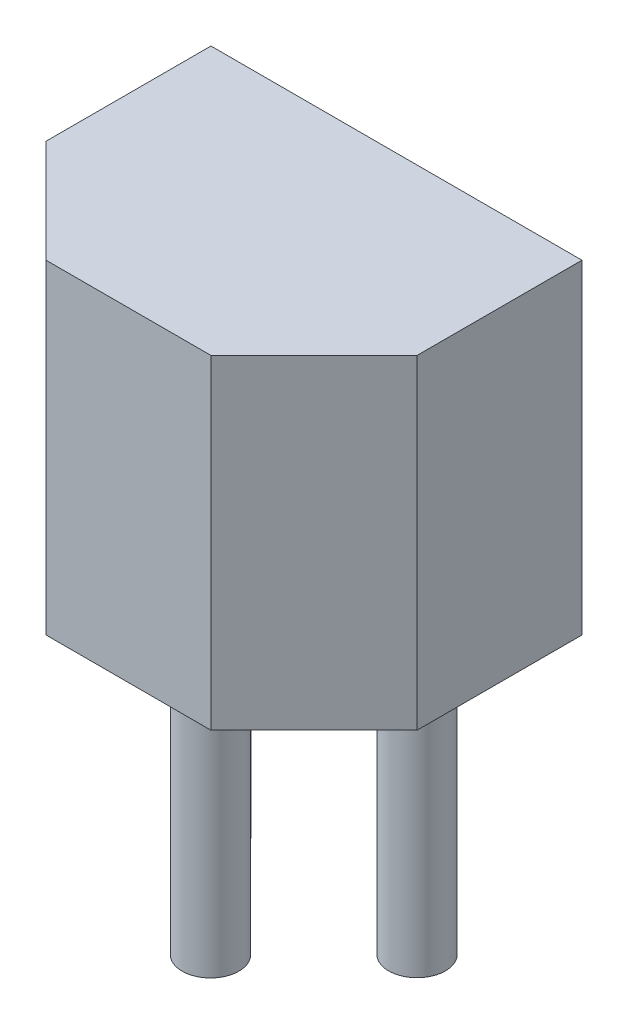
SolidWorks part; units mm, degrees
ref_plane "Front Plane" through (0, 0, 0) normal (0, 0, 1) x (1, 0, 0)
ref_plane "Top Plane" through (0, 0, 0) normal (0, 1, 0) x (1, 0, 0)
ref_plane "Right Plane" through (0, 0, 0) normal (1, 0, 0) x (0, 0, -1)
sketch "Sketch1" plane through (0, 0, 0) normal (0, 1, 0) x (1, 0, 0)
  line L0 (-1.016, -1.016) -> (0.254, -2.286)
  line L1 (-1.016, -1.016) -> (-1.016, 1.016)
  line L2 (-1.016, 1.016) -> (3.556, 1.016)
  line L3 (0.254, -2.286) -> (2.286, -2.286)
  line L4 (2.286, -2.286) -> (3.556, -1.016)
  line L5 (3.556, -1.016) -> (3.556, 1.016)
extrude "Boss-Extrude1" add sketch "Sketch1" along normal blind 4
sketch "Sketch2" plane through (0, 0, 0) normal (0, -1, 0) x (1, 0, 0)
  line L0 (0, 0) -> (2.54, 0) construction
  line L1 (1.27, 0) -> (1.27, 2.6699) construction
  circle A0 centre (0, 0) radius 0.35
  circle A1 centre (2.54, 0) radius 0.35
  circle A2 centre (1.27, 1.2756) radius 0.35
  dimension "D2" = 0.7
  dimension "D1" = 2.54
  dimension "D3" = 1.8
extrude "Boss-Extrude2" add sketch "Sketch2" along normal blind 3.41
ref_plane "Board Plane" through (0, -0.5, 0) normal (0, 1, 0) x (-1, 0, 0)
sketch "Component_Outline" plane through (0, -0.5, 0) normal (0, 1, 0) x (-1, 0, 0)
  line L0 (1.016, -1.016) -> (-3.556, -1.016)
  line L1 (-3.556, -1.016) -> (-3.556, 1.016)
  line L2 (-3.556, 1.016) -> (-2.286, 2.286)
  line L3 (-2.286, 2.286) -> (-0.254, 2.286)
  line L4 (-0.254, 2.286) -> (1.016, 1.016)
  line L5 (1.016, 1.016) -> (1.016, -1.016)
  point P10 (0, 0)
